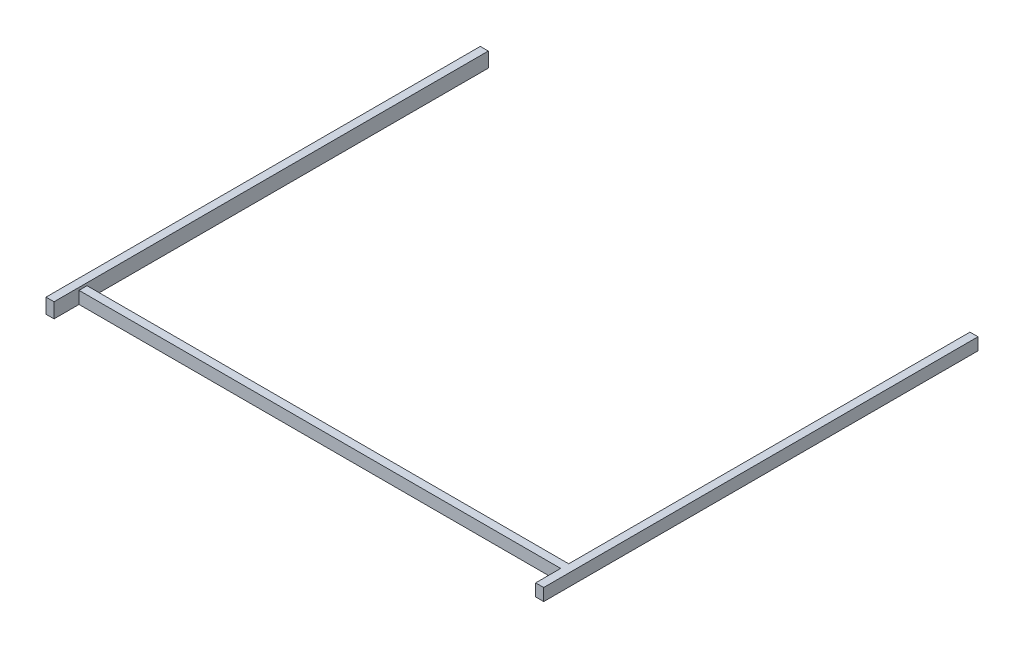
SolidWorks part; units mm, degrees
ref_plane "Front Plane" through (0, 0, 0) normal (0, 0, 1) x (1, 0, 0)
ref_plane "Top Plane" through (0, 0, 0) normal (0, 1, 0) x (1, 0, 0)
ref_plane "Right Plane" through (0, 0, 0) normal (1, 0, 0) x (0, 0, -1)
sketch "Sketch1" plane through (0, 0, 0) normal (0, 0, 1) x (1, 0, 0)
  line L0 (-127599.8456, -152.4) -> (-127574.4456, -152.4) construction
  line L1 (-140349.7617, 32.4) -> (-140449.7617, 32.4)
  line L2 (-140349.7617, 32.4) -> (-140349.7617, -152.4)
  line L3 (-140349.7617, -152.4) -> (-140449.7617, -152.4)
  line L4 (-140449.7617, 32.4) -> (-140449.7617, -152.4)
  line L6 (-134349.7617, 0) -> (-134249.7617, 0)
  line L7 (-134349.7617, 0) -> (-134349.7617, -152.4)
  line L8 (-134349.7617, -152.4) -> (-134249.7617, -152.4)
  line L9 (-134249.7617, 0) -> (-134249.7617, -152.4)
  line L14 (-140349.7617, -120) -> (-140349.7617, -220) construction
  line L15 (-134349.7617, -120) -> (-134349.7617, -220) construction
  dimension "D1" = 100
  dimension "D2" = 100
extrude "Extrude1" add sketch "Sketch1" along normal up to vertex (5387.4779 mm away)
sketch "Sketch2" plane through (-134349.7617, 0, 0) normal (-1, 0, 0) x (0, 0, 1)
  line L0 (5409.9984, 0) -> (0, 0) construction
  line L1 (5098.7214, 0) -> (4998.7214, 0)
  line L2 (5098.7214, 0) -> (5098.7214, -152.4)
  line L3 (5098.7214, -152.4) -> (4998.7214, -152.4)
  line L4 (4998.7214, 0) -> (4998.7214, -152.4)
  line L5 (5409.9984, -152.4) -> (0, -152.4) construction
  dimension "D1" = 100
extrude "Extrude2" add sketch "Sketch2" along normal up to surface (6000 mm away) up to face at (-140349.7617, -60, 2704.9992)
